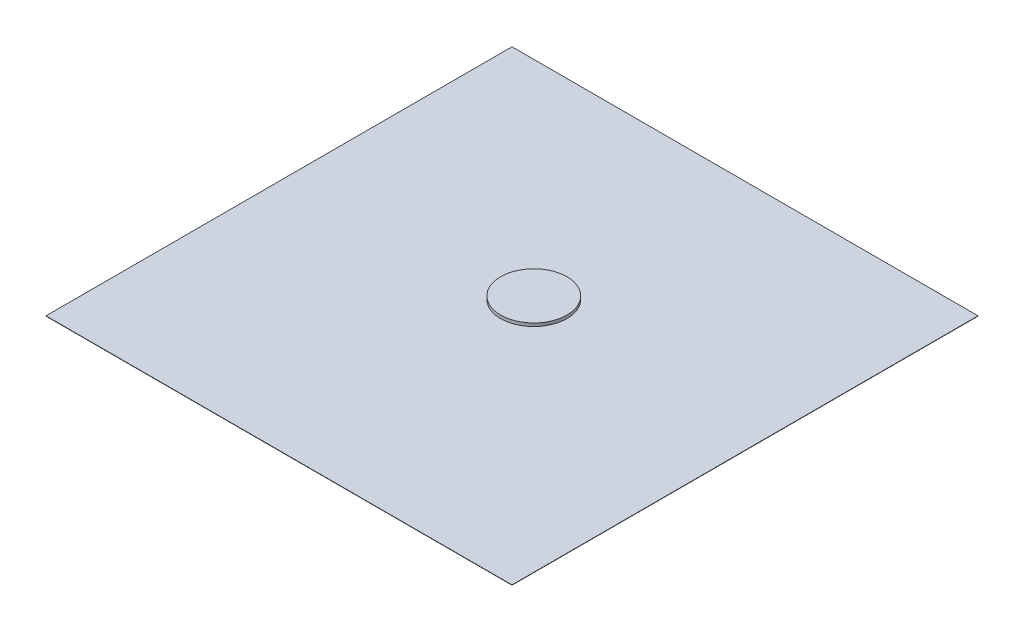
SolidWorks part; units mm, degrees
material "3.0205 (EN-AW 1200)"
ref_plane "Front Plane" through (0, 0, 0) normal (0, 0, 1) x (1, 0, 0)
ref_plane "Top Plane" through (0, 0, 0) normal (0, 1, 0) x (1, 0, 0)
ref_plane "Right Plane" through (0, 0, 0) normal (1, 0, 0) x (0, 0, -1)
sketch "Sketch1" plane through (0, 0, 0) normal (0, 1, 0) x (1, 0, 0)
  line L1 (0, 0) -> (1500, 0)
  line L2 (0, 0) -> (0, 1500)
  line L3 (0, 1500) -> (1500, 1500)
  line L4 (1500, 0) -> (1500, 1500)
extrude "Boss-Extrude1" add sketch "Sketch1" along normal blind 1
sketch "Sketch2" plane through (0, 1, 0) normal (0, 1, 0) x (1, 0, 0)
  circle A0 centre (739.528, 830.6344) radius 106.8144
extrude "Boss-Extrude2" add sketch "Sketch2" along normal blind 10
